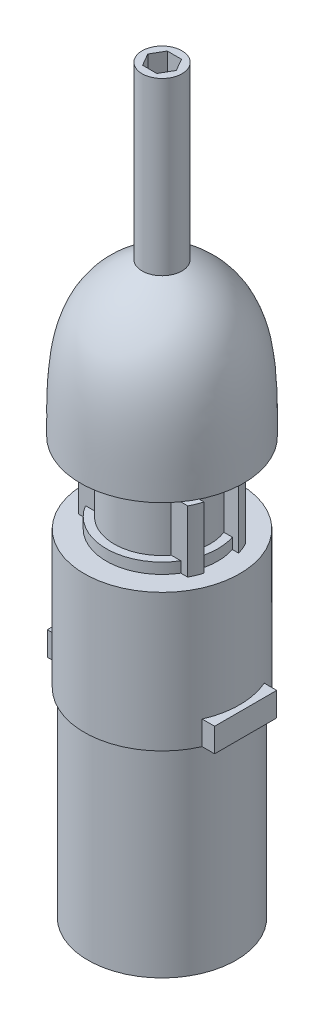
SolidWorks part; units mm, degrees
ref_plane "Front Plane" through (0, 0, 0) normal (0, 0, 1) x (1, 0, 0)
ref_plane "Top Plane" through (0, 0, 0) normal (0, 1, 0) x (1, 0, 0)
ref_plane "Right Plane" through (0, 0, 0) normal (1, 0, 0) x (0, 0, -1)
sketch "Sketch1" plane through (0, 0, 0) normal (0, 1, 0) x (1, 0, 0)
  circle A0 centre (0, 0) radius 14
  dimension "D1" = 28
extrude "Boss-Extrude1" add sketch "Sketch1" along normal blind 2.7
sketch "Sketch2" plane through (0, 0, 0) normal (0, 1, 0) x (1, 0, 0)
  circle A0 centre (0, 0) radius 12
  dimension "D1" = 24
extrude "Boss-Extrude2" add sketch "Sketch2" along normal blind 15.5
sketch "Sketch3" plane through (0, 0, 0) normal (0, 1, 0) x (1, 0, 0)
  line L0 (13.6999, 7.25) -> (-13.6999, 7.25)
  line L1 (-15.5, -7.25) -> (15.5, -7.25) construction
  line L2 (-15.5, -7.25) -> (-15.5, 7.25) construction
  line L3 (-15.5, 7.25) -> (15.5, 7.25) construction
  line L4 (15.5, -7.25) -> (15.5, 7.25) construction
  line L5 (-15.5, -7.25) -> (15.5, 7.25) construction
  line L6 (-15.5, 7.25) -> (15.5, -7.25) construction
  line L7 (-15.5, -4.35) -> (15.5, -4.35) construction
  line L8 (-15.5, -4.35) -> (-15.5, 4.35) construction
  line L9 (-15.5, 4.35) -> (15.5, 4.35) construction
  line L10 (15.5, -4.35) -> (15.5, 4.35) construction
  line L11 (-15.5, -4.35) -> (15.5, 4.35) construction
  line L12 (-15.5, 4.35) -> (15.5, -4.35) construction
  line L13 (14.8771, 4.35) -> (-14.8771, 4.35)
  line L14 (14.8771, -4.35) -> (-14.8771, -4.35)
  line L15 (13.6999, -7.25) -> (-13.6999, -7.25)
  circle A0 centre (0, 0) radius 15.5 construction
  arc A1 (-14.8771, 4.35) -> (-13.6999, 7.25) centre (0, 0) cw
  arc A2 (13.6999, 7.25) -> (14.8771, 4.35) centre (0, 0) cw
  arc A3 (14.8771, -4.35) -> (13.6999, -7.25) centre (0, 0) cw
  arc A4 (-13.6999, -7.25) -> (-14.8771, -4.35) centre (0, 0) cw
  point P0 (0, 0)
  point P5 (0, 0)
  dimension "D1" = 14.5
  dimension "D2" = 31
  dimension "D3" = 8.7
extrude "Boss-Extrude3" add sketch "Sketch3" along normal blind 15.5 contours A2 L0 A1 L13 | A4 L15 A3 L14
sketch "Sketch4" plane through (0, 0, 0) normal (0, -1, 0) x (1, 0, 0)
  circle A0 centre (0, 0) radius 19.5
  dimension "D1" = 39
extrude "Boss-Extrude4" add sketch "Sketch4" along normal blind 34.5
sketch "Sketch5" plane through (0, -34.5, 0) normal (0, -1, 0) x (1, 0, 0)
  line L1 (-21, -7.8) -> (21, -7.8)
  line L2 (-21, -7.8) -> (-21, 7.8)
  line L3 (-21, 7.8) -> (21, 7.8)
  line L4 (21, -7.8) -> (21, 7.8)
  line L5 (-21, -7.8) -> (21, 7.8) construction
  line L6 (-21, 7.8) -> (21, -7.8) construction
  point P0 (0, 0)
  dimension "D1" = 15.6
  dimension "D2" = 42
extrude "Boss-Extrude5" add sketch "Sketch5" against normal blind 6
sketch "Sketch6" plane through (0, -34.5, 0) normal (0, -1, 0) x (1, 0, 0)
  circle A0 centre (0, 0) radius 18.6
  dimension "D1" = 37.2
extrude "Boss-Extrude6" add sketch "Sketch6" along normal blind 50 separate body
sketch "Sketch7" plane through (0, 0, 0) normal (0, 0, 1) x (1, 0, 0)
  line L2 (0, 15.5) -> (0, 20.2)
  line L3 (0, 20.2) -> (0, 101.5)
  line L4 (0, 101.5) -> (5, 101.5)
  line L5 (5, 101.5) -> (5, 58.6)
  line L6 (0, 15.5) -> (7.5, 15.5)
  line L7 (7.5, 15.5) -> (7.5, 20.2)
  line L8 (7.5, 20.2) -> (20.5, 20.2)
  line L9 (16, 49.2) -> (16, 20.2) construction
  line L10 (16, 49.2) -> (0, 49.2) construction
  spline S0 degree 3 poles (20.5, 20.2) (20.4745, 37.4327) (20.8661, 50.9965) (5, 58.6) knots 0 0 0 0 1 1 1 1
  dimension "D1" = 4.7
  dimension "D2" = 81.3
  dimension "D3" = 5
  dimension "D4" = 42.9
  dimension "D5" = 7.5
  dimension "D6" = 20.5
  dimension "D7" = 29
  dimension "D8" = 16
revolve "Revolve1" add sketch "Sketch7" angle 360 about L3
sketch "Sketch8" plane through (0, 0, 0) normal (0, 0, 1) x (1, 0, 0)
  line L0 (5, 58.6) -> (-5, 58.6) construction
  line L1 (5, 58.6) -> (-5, 58.6)
split "Split1" trim tools "Sketch8" bodies to split 107 resulting bodies 108 109
sketch "Sketch9" plane through (0, 101.5, 0) normal (0, 1, 0) x (1, 0, 0)
  line L1 (3.5796, 0) -> (1.7898, 3.1)
  line L2 (1.7898, 3.1) -> (-1.7898, 3.1)
  line L3 (-1.7898, 3.1) -> (-3.5796, 0)
  line L4 (-3.5796, 0) -> (-1.7898, -3.1)
  line L5 (-1.7898, -3.1) -> (1.7898, -3.1)
  line L6 (1.7898, -3.1) -> (3.5796, 0)
  circle A0 centre (0, 0) radius 3.1 construction
extrude "Cut-Extrude1" cut sketch "Sketch9" against normal blind 11.2
equation "\"m3_hole\"= 3.5"
equation "\"m3_washer\"= 7.3"
equation "\"m3_nut\"= 5.3"
equation "\"guide_width\"= 10.0"
equation "\"guide_length\"= 65.0"
equation "\"guide_tab_length\" = 10.0"
equation "\"guide_tab_width\" = 9.0"
equation "\"guide_thickness\" = 12.0"
equation "\"grinder_od\"= 52.0"
equation "\"grinder_id\"= 45.5"
equation "\"grinder_adjust_od\" = 58.0"
equation "\"funnel_width_from_adjust_ring\" = 13.0"
equation "\"drill_contact_diameter_small\" = 24.0"
equation "\"drill_contact_diameter_medium\" = 28.0"
equation "\"drill_contact_diameter_large\" = 39.0"
equation "\"drill_contact_diameter_tab\" = 31.0"
equation "\"D1@Sketch2\"=\"drill_contact_diameter_small\""
equation "\"D1@Sketch1\"=\"drill_contact_diameter_medium\""
equation "\"D2@Sketch3\"=\"drill_contact_diameter_tab\""
equation "\"drill_contact_ow_tab\" = 14.5"
equation "\"drill_contact_iw_tab\" = 8.7"
equation "\"D3@Sketch3\"=\"drill_contact_iw_tab\""
equation "\"D1@Sketch3\"=\"drill_contact_ow_tab\""
equation "\"drill_contact_small_height\" = 15.5"
equation "\"D1@Boss-Extrude3\"=\"drill_contact_small_height\""
equation "\"drill_contact_large_height\" = 34.5"
